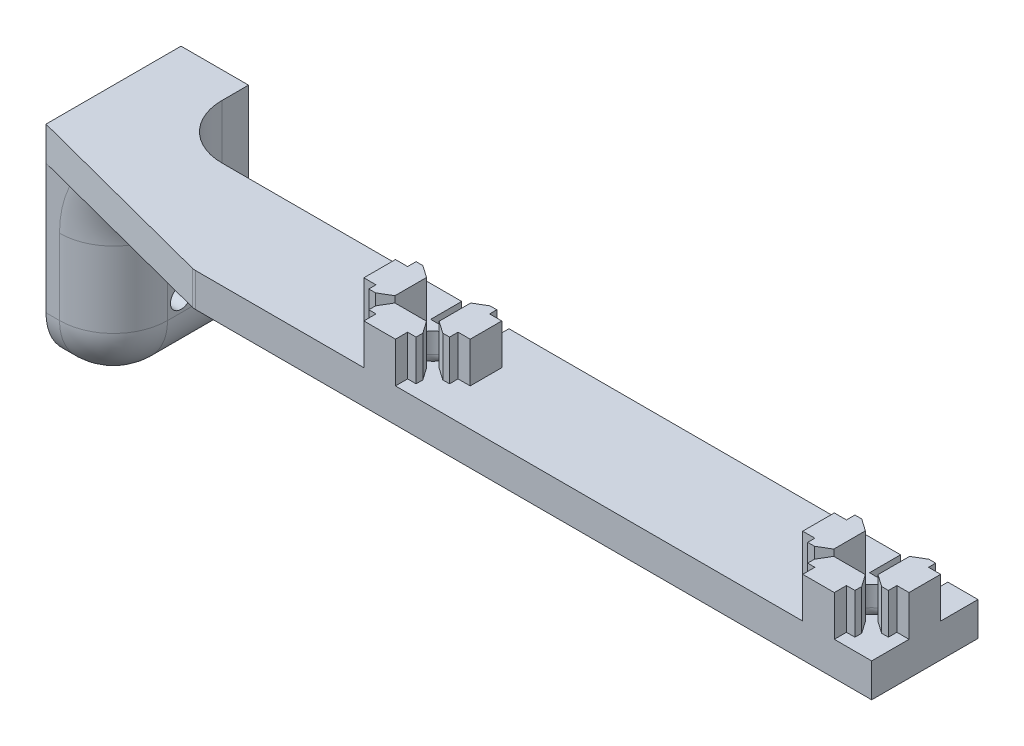
SolidWorks part; units mm, degrees
ref_plane "Front Plane" through (0, 0, 0) normal (0, 0, 1) x (1, 0, 0)
ref_plane "Top Plane" through (0, 0, 0) normal (0, 1, 0) x (1, 0, 0)
ref_plane "Right Plane" through (0, 0, 0) normal (1, 0, 0) x (0, 0, -1)
sketch "Sketch1" plane through (0, 0, 0) normal (0, 1, 0) x (1, 0, 0)
  line L0 (-2.9718, 10) -> (-2.9718, 7.714)
  line L1 (-10, 10) -> (10, 10)
  line L2 (-10, 10) -> (-10, -10)
  line L3 (-10, -10) -> (10, -10)
  line L4 (10, 10) -> (10, -10)
  line L5 (-10, 10) -> (10, -10) construction
  line L6 (-10, -10) -> (10, 10) construction
  line L7 (-2.9718, 10) -> (2.9718, 10) construction
  line L8 (-2.9718, 10) -> (-2.9718, 4.158) construction
  line L9 (-2.9718, 4.158) -> (2.9718, 4.158) construction
  line L10 (2.9718, 10) -> (2.9718, 4.158) construction
  line L11 (-4.5679, 7.714) -> (4.3221, 7.714) construction
  line L12 (-4.5679, 7.714) -> (-4.5679, 6.444) construction
  line L13 (-4.5679, 6.444) -> (4.3221, 6.444) construction
  line L14 (4.3221, 7.714) -> (4.3221, 6.444) construction
  line L15 (-4.5679, 7.714) -> (4.3221, 6.444) construction
  line L16 (-4.5679, 6.444) -> (4.3221, 7.714) construction
  line L17 (-2.9718, 7.714) -> (-4.5679, 7.714)
  line L18 (-4.5679, 7.714) -> (-4.5679, 6.444)
  line L19 (-4.5679, 6.444) -> (-2.9718, 4.158)
  line L20 (-2.9718, 4.158) -> (2.9718, 4.158)
  line L21 (2.9718, 4.158) -> (4.3221, 6.444)
  line L22 (4.3221, 6.444) -> (4.3221, 7.714)
  line L23 (4.3221, 7.714) -> (2.9718, 7.714)
  line L24 (2.9718, 7.714) -> (2.9718, 10)
  line L25 (2.9718, 10) -> (-2.9718, 10)
  line L26 (4.158, -2.9718) -> (4.158, 2.9718)
  line L27 (4.158, 2.9718) -> (6.444, 4.3221)
  line L28 (6.444, 4.3221) -> (7.714, 4.3221)
  line L29 (7.714, 4.3221) -> (7.714, 2.9718)
  line L30 (7.714, 2.9718) -> (10, 2.9718)
  line L31 (10, -2.9718) -> (10, 2.9718) construction
  line L32 (10, 2.9718) -> (10, -2.9718)
  line L33 (10, -2.9718) -> (7.714, -2.9718)
  line L34 (7.714, -2.9718) -> (7.714, -4.5679)
  line L35 (7.714, -4.5679) -> (6.444, -4.5679)
  line L36 (6.444, -4.5679) -> (4.158, -2.9718)
  line L37 (2.9718, -10) -> (-2.9718, -10) construction
  line L38 (4.5679, -6.444) -> (2.9718, -4.158)
  line L39 (4.5679, -7.714) -> (4.5679, -6.444)
  line L40 (2.9718, -7.714) -> (4.5679, -7.714)
  line L41 (2.9718, -10) -> (2.9718, -7.714)
  line L42 (-2.9718, -10) -> (2.9718, -10)
  line L43 (-2.9718, -7.714) -> (-2.9718, -10)
  line L44 (-4.3221, -7.714) -> (-2.9718, -7.714)
  line L45 (-4.3221, -6.444) -> (-4.3221, -7.714)
  line L46 (-2.9718, -4.158) -> (-4.3221, -6.444)
  line L47 (2.9718, -4.158) -> (-2.9718, -4.158)
  line L48 (-10, 2.9718) -> (-10, -2.9718) construction
  line L49 (-10, -2.9718) -> (-10, 2.9718)
  line L50 (-7.714, -2.9718) -> (-10, -2.9718)
  line L51 (-7.714, -4.3221) -> (-7.714, -2.9718)
  line L52 (-6.444, -4.3221) -> (-7.714, -4.3221)
  line L53 (-4.158, -2.9718) -> (-6.444, -4.3221)
  line L54 (-4.158, 2.9718) -> (-4.158, -2.9718)
  line L55 (-6.444, 4.5679) -> (-4.158, 2.9718)
  line L56 (-7.714, 4.5679) -> (-6.444, 4.5679)
  line L57 (-7.714, 2.9718) -> (-7.714, 4.5679)
  line L58 (-10, 2.9718) -> (-7.714, 2.9718)
  point P0 (0, 0)
  point P12 (0, 4.158)
  point P13 (-0.1229, 7.079)
  dimension "D1" = 20
  dimension "D2" = 20
  dimension "D4" = 5.9436
  dimension "D5" = 10
  dimension "D6" = 5.842
  dimension "D7" = 2.286
  dimension "D8" = 3.556
  dimension "D9" = 8.89
extrude "Boss-Extrude1" add sketch "Sketch1" along normal blind 7.62 contours L23 L24 L1 L0 L17 L18 L19 L20 L21 L22 | L26 L27 L28 L29 L30 L32 L33 L34 L35 L36 | L49 L58 L57 L56 L55 L54 L53 L52 L51 L50 | L38 L47 L46 L45 L44 L43 L42 L41 L40 L39
sketch "Sketch2" plane through (0, 0, 0) normal (0, -1, 0) x (1, 0, 0)
  line L1 (10, -10) -> (-155.1, -10)
  line L2 (10, -10) -> (10, 10)
  line L3 (10, 10) -> (-155.1, 10)
  line L4 (-155.1, -10) -> (-155.1, 10)
  line L5 (10, -10) -> (-155.1, 10) construction
  line L6 (10, 10) -> (-155.1, -10) construction
  line L7 (-2.9718, -10) -> (2.9718, -10) construction
  line L8 (10, -2.9718) -> (10, 2.9718) construction
  dimension "D1" = 165.1
  dimension "D2" = 20
  dimension "D3" = 0
  dimension "D4" = 0
extrude "Boss-Extrude2" add sketch "Sketch2" along normal blind 6.35
pattern_linear "LPattern2" count 2 spacing 82.55 along (-1, 0, 0) of "Boss-Extrude1"
sketch "Sketch4" plane through (0, -6.35, 0) normal (0, -1, 0) x (-1, 0, 0)
  line L0 (155.1, 10) -> (155.1, -0.2108) construction
  line L1 (155.1, -10) -> (155.1, 10) construction
  line L2 (155.1, -10) -> (117.5588, -10)
  line L3 (-10, -10) -> (155.1, -10) construction
  line L4 (117.5588, -10) -> (155.1, -0.2108)
  line L5 (155.1, -0.2108) -> (155.1, -10)
  dimension "D1" = 10.2108
  dimension "D2" = 37.5412
extrude "Cut-Extrude1" cut sketch "Sketch4" against normal through all
fillet "Fillet1" radius 2.54 1 edges at (-117.5588, -3.175, 10)
sketch "Sketch13" plane through (0, 0, 0) normal (0, 1, 0) x (1, 0, 0)
  line L0 (-86.708, -2.9718) -> (-88.994, -4.3221) construction
  line L1 (4.158, 2.9718) -> (-4.158, 2.9718) construction
  line L2 (4.158, 2.9718) -> (4.158, -2.9718) construction
  line L3 (4.158, -2.9718) -> (-4.158, -2.9718) construction
  line L4 (-4.158, 2.9718) -> (-4.158, -2.9718) construction
  line L5 (-78.392, 2.9718) -> (-86.708, 2.9718) construction
  line L6 (-78.392, 2.9718) -> (-78.392, -2.9718) construction
  line L7 (-78.392, -2.9718) -> (-86.708, -2.9718) construction
  line L8 (-86.708, 2.9718) -> (-86.708, -2.9718) construction
  line L9 (-86.708, 2.9718) -> (-86.708, -2.9718) construction
  line L10 (-82.55, 2.9718) -> (-82.55, -2.9718) construction
  circle A0 centre (0, 0) radius 3.5
  circle A1 centre (-82.55, 0) radius 3.5
  dimension "D1" = 7
  dimension "D2" = 7
extrude "Cut-Extrude5" cut sketch "Sketch13" against normal through all
fillet "Fillet6" radius 2.54 2 edges at (0, -6.35, 3.5) (-82.55, -6.35, 3.5)
sketch "Sketch14" plane through (0, 7.62, 0) normal (0, 1, 0) x (1, 0, 0)
  line L0 (-85.5218, 4.158) -> (-79.5782, 4.158) construction
  line L5 (4.3221, 10) -> (-4.5679, 10)
  line L6 (4.3221, 10) -> (4.3221, 4.158)
  line L7 (4.3221, 4.158) -> (-4.5679, 4.158)
  line L8 (-4.5679, 10) -> (-4.5679, 4.158)
  line L9 (-78.2279, 4.158) -> (-87.1179, 4.158)
  line L10 (-78.2279, 4.158) -> (-78.2279, 10)
  line L11 (-78.2279, 10) -> (-87.1179, 10)
  line L12 (-87.1179, 4.158) -> (-87.1179, 10)
  line L13 (-78.2279, 4.158) -> (-87.1179, 10) construction
  line L14 (-78.2279, 10) -> (-87.1179, 4.158) construction
  line L15 (-85.5218, 10) -> (-79.5782, 10) construction
  line L16 (-87.1179, 7.714) -> (-87.1179, 6.444) construction
  line L17 (-78.2279, 6.444) -> (-78.2279, 7.714) construction
  line L18 (4.3221, 6.444) -> (4.3221, 7.714) construction
  line L19 (-4.5679, 7.714) -> (-4.5679, 6.444) construction
  point P0 (-82.6729, 7.079)
  point P19 (-87.1179, 7.079)
  dimension "D1" = 0
  dimension "D2" = 0
  dimension "D3" = 0
  dimension "D4" = 0
  dimension "D5" = 0
  dimension "D6" = 0
extrude "Cut-Extrude6" cut sketch "Sketch14" against normal through all
sketch "Sketch15" plane through (-155.1, 0, 0) normal (-1, 0, 0) x (0, 0, 1)
  line L0 (0.2108, -6.35) -> (-10, -6.35) construction
  line L10 (0.2108, 0) -> (-25.1892, 0)
  line L11 (0.2108, 0) -> (0.2108, -40.894)
  line L12 (0.2108, -40.894) -> (-25.1892, -40.894)
  line L13 (-25.1892, 0) -> (-25.1892, -40.894)
  dimension "D1" = 34.544
  dimension "D2" = 25.4
extrude "Boss-Extrude3" add sketch "Sketch15" against normal blind 12.7
fillet "Fillet15" radius 10.16 1 edges at (-142.4, -6.35, -4.8946)
fillet "Fillet16" radius 10.16 1 edges at (-142.4, -8.255, -10)
fillet "Fillet17" radius 10.16 1 edges at (-142.4, -40.894, -12.4892)
fillet "Fillet18" radius 10.16 4 edges at (-153.83, -40.894, 0.2108) (-145.3758, -37.9182, 0.2108) (-139.4242, -9.3258, 0.2108) (-142.4, -23.622, 0.2108)
sketch "Sketch18" plane through (-155.1, 0, 0) normal (-1, 0, 0) x (0, 0, 1)
  line L1 (-25.1892, -40.894) -> (-12.4892, -40.894) construction
  line L2 (-25.1892, -40.894) -> (-25.1892, -28.194) construction
  line L3 (-25.1892, -28.194) -> (-12.4892, -28.194) construction
  line L4 (-12.4892, -40.894) -> (-12.4892, -28.194) construction
  circle A0 centre (-12.4892, -28.194) radius 1.9844
  dimension "D3" = 3.9688
  dimension "D1" = 12.7
  dimension "D2" = 12.7
extrude "Cut-Extrude9" cut sketch "Sketch18" against normal up to surface (12.7 mm away) up to face at (-142.4, -15.748, -18.4328)
